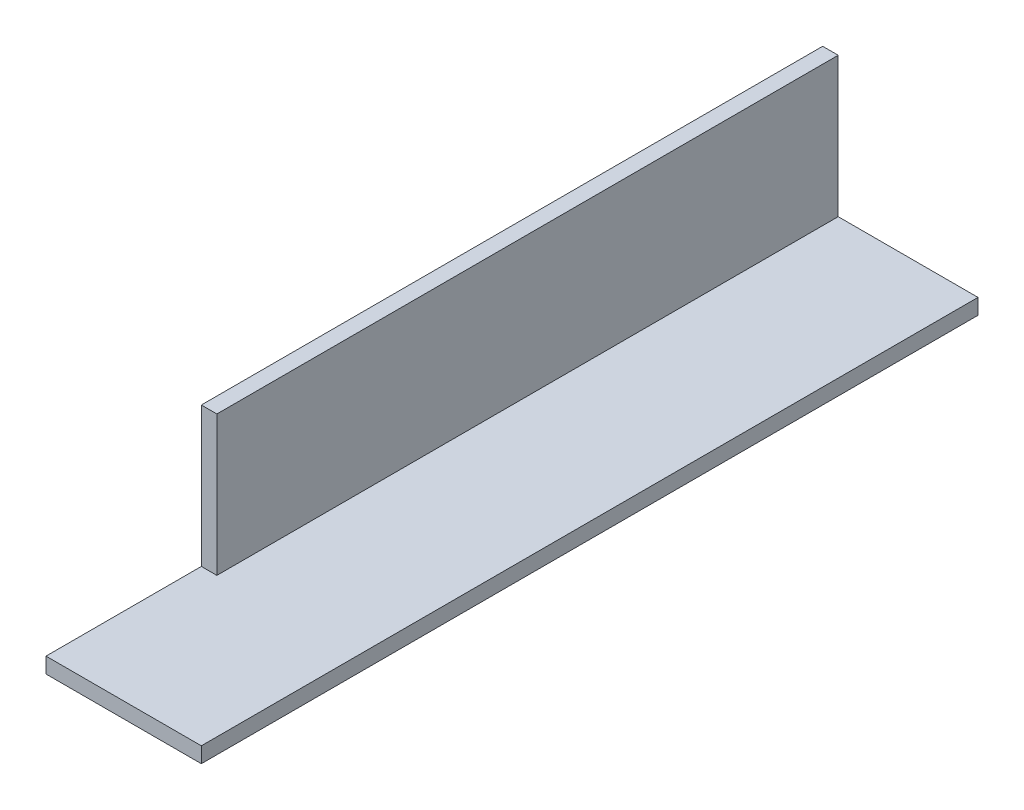
SolidWorks part; units mm, degrees
ref_plane "Front Plane" through (0, 0, 0) normal (0, 0, 1) x (1, 0, 0)
ref_plane "Top Plane" through (0, 0, 0) normal (0, 1, 0) x (1, 0, 0)
ref_plane "Right Plane" through (0, 0, 0) normal (1, 0, 0) x (0, 0, -1)
sketch "Sketch1" plane through (0, 0, 0) normal (0, 0, 1) x (1, 0, 0)
  line L0 (0, 0) -> (0, 20)
  line L1 (0, 0) -> (20, 0)
  line L2 (2, 2) -> (20, 2)
  line L3 (2, 2) -> (2, 20)
  line L4 (0, 20) -> (2, 20)
  line L5 (20, 2) -> (20, 0)
  dimension "D1" = 20
  dimension "D2" = 20
  dimension "D3" = 2
extrude "Boss-Extrude1" add sketch "Sketch1" along normal blind 100
sketch "Sketch3" plane through (2, 0, 0) normal (1, 0, 0) x (0, 0, -1)
  line L0 (-100, 20) -> (-100, 2)
  line L1 (-100, 2) -> (-80, 2)
  line L2 (-100, 2) -> (0, 2) construction
  line L3 (-80, 2) -> (-80, 20)
  line L4 (-100, 20) -> (0, 20) construction
  line L5 (-80, 20) -> (-100, 20)
  dimension "D1" = 20
extrude "Cut-Extrude2" cut sketch "Sketch3" against normal through all
